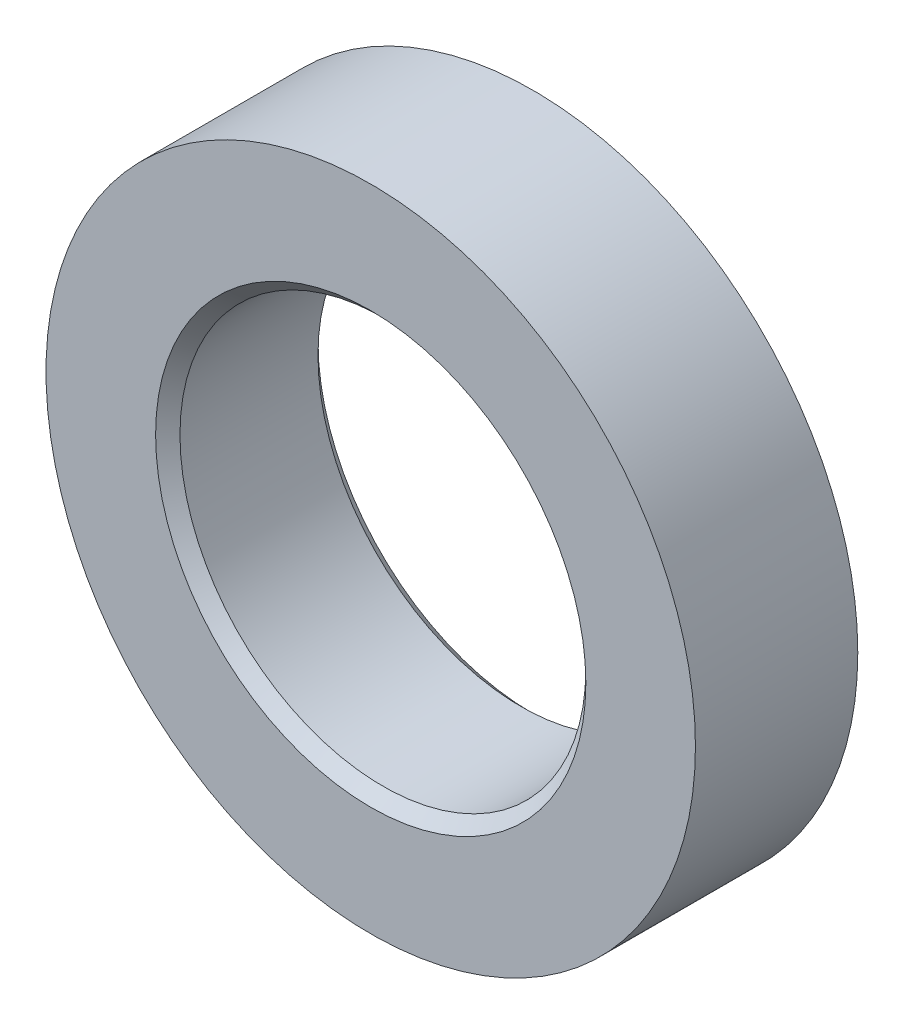
SolidWorks part; units mm, degrees
material "Alloy Steel (SS)"
ref_plane "Front Plane" through (0, 0, 0) normal (0, 0, 1) x (1, 0, 0)
ref_plane "Top Plane" through (0, 0, 0) normal (0, 1, 0) x (1, 0, 0)
ref_plane "Right Plane" through (0, 0, 0) normal (1, 0, 0) x (0, 0, -1)
sketch "Sketch1" plane through (0, 0, 0) normal (0, 0, 1) x (1, 0, 0)
  circle A0 centre (0, 0) radius 5
  circle A1 centre (0, 0) radius 8
  dimension "D1" = 10
  dimension "D2" = 3
extrude "Boss-Extrude1" add sketch "Sketch1" along normal blind 4
chamfer "Chamfer1" distance 0.3 angle 45 2 edges at (5, 0, 0) (5, 0, 4)
